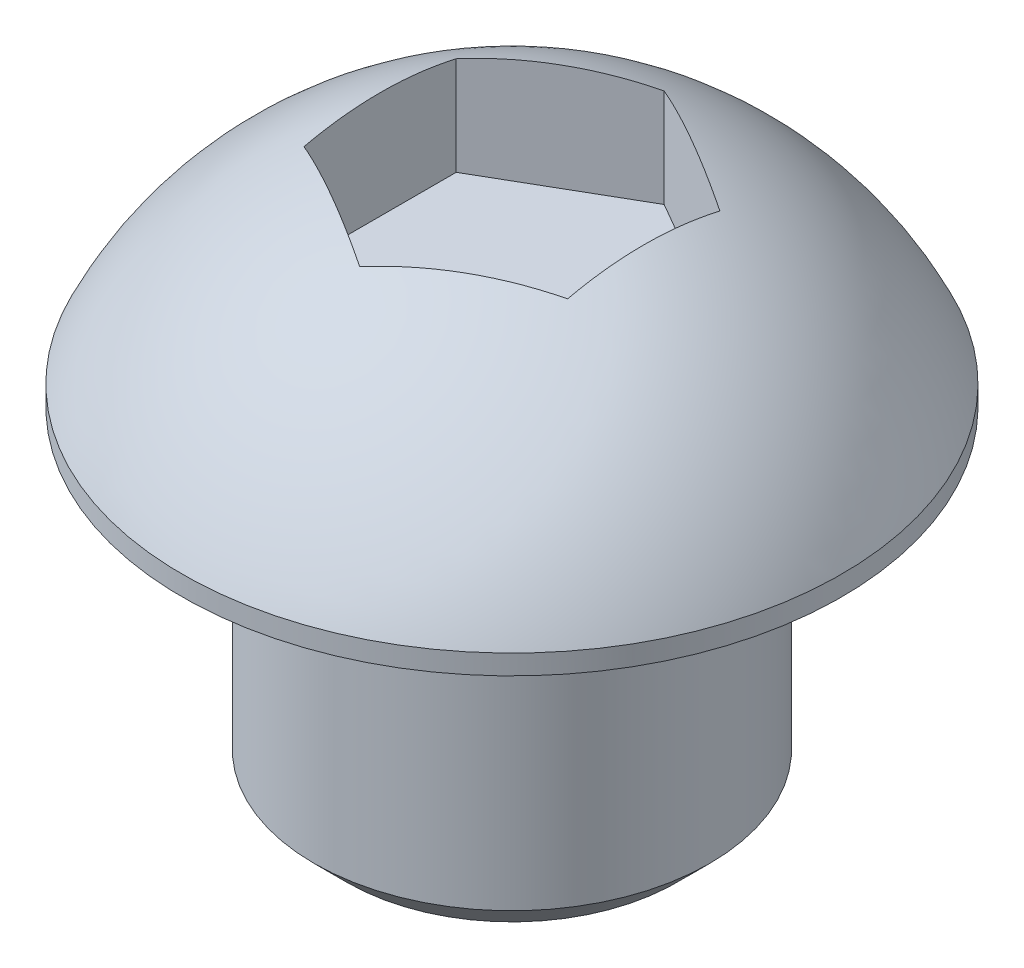
SolidWorks part; units mm, degrees
material "1.6523 (20NiCrMoS2-2)"
ref_plane "Front Plane" through (0, 0, 0) normal (0, 0, 1) x (1, 0, 0)
ref_plane "Top Plane" through (0, 0, 0) normal (0, 1, 0) x (1, 0, 0)
ref_plane "Right Plane" through (0, 0, 0) normal (1, 0, 0) x (0, 0, -1)
sketch "Sketch1" plane through (0, 0, 0) normal (0, 1, 0) x (1, 0, 0)
  circle A0 centre (0, 0) radius 3
  circle A1 centre (0, 0) radius 5
  dimension "D1" = 6
  dimension "D2" = 10
extrude "Boss-Extrude3" add sketch "Sketch1" against normal blind 5 contours A0
sketch "Sketch3" plane through (0, 0, 0) normal (0, 0, 1) x (1, 0, 0)
  line L0 (-5, 0) -> (-5, 0.3)
  line L1 (5, 0) -> (-5, 0) construction
  line L4 (0, -2) -> (0, 2.3599) construction
  line L5 (-5, 0) -> (0, 0)
  line L6 (0, 3.5036) -> (0, 0)
  arc A0 (-5, 0.3) -> (0, 3.5036) centre (0, -2) cw
  dimension "D1" = 10
  dimension "D2" = 0.3
  dimension "D3" = 2
revolve "Revolve2" add sketch "Sketch3" angle 360 about L4
chamfer "Chamfer2" distance 0.5 angle 45 1 edges at (0, -5, 3)
ref_plane "Plane1" through (0, 3.5036, 0) normal (0, 1, 0) x (1, 0, 0)
sketch "Sketch4" plane through (0, 3.5036, 0) normal (0, 1, 0) x (1, 0, 0)
  line L1 (0, 2.3094) -> (-2, 1.1547)
  line L2 (-2, 1.1547) -> (-2, -1.1547)
  line L3 (-2, -1.1547) -> (0, -2.3094)
  line L4 (0, -2.3094) -> (2, -1.1547)
  line L5 (2, -1.1547) -> (2, 1.1547)
  line L6 (2, 1.1547) -> (0, 2.3094)
  circle A0 centre (0, 0) radius 2 construction
  dimension "D1" = 4
extrude "Cut-Extrude2" cut sketch "Sketch4" against normal blind 2
